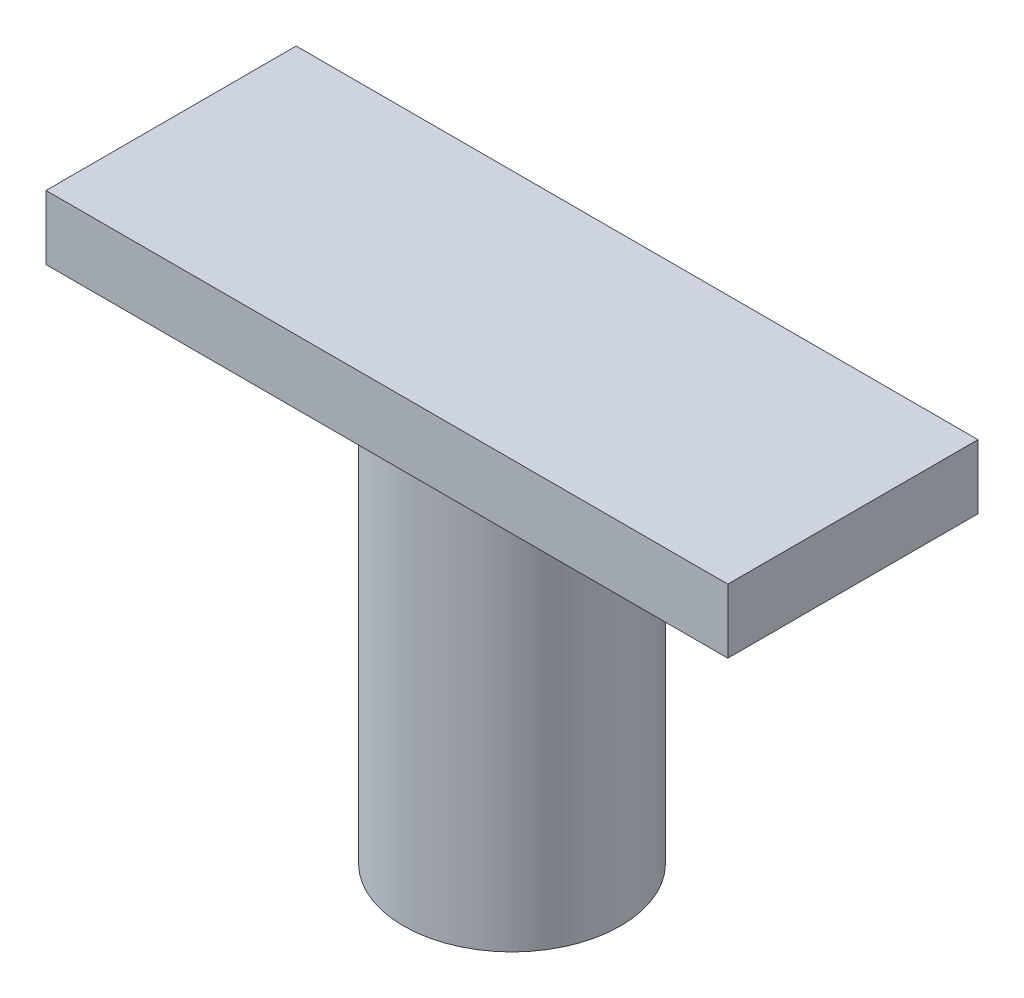
SolidWorks part; units mm, degrees
ref_plane "Front Plane" through (0, 0, 0) normal (0, 0, 1) x (1, 0, 0)
ref_plane "Top Plane" through (0, 0, 0) normal (0, 1, 0) x (1, 0, 0)
ref_plane "Right Plane" through (0, 0, 0) normal (1, 0, 0) x (0, 0, -1)
sketch "Sketch1" plane through (0, 0, 0) normal (0, 1, 0) x (1, 0, 0)
  circle A0 centre (22.7298, -8.2396) radius 16.9166
extrude "Boss-Extrude1" add sketch "Sketch1" along normal blind 64
sketch "Sketch2" plane through (0, 64, 0) normal (0, 1, 0) x (1, 0, 0)
  line L1 (-30.4017, -27.7334) -> (75.8613, -27.7334)
  line L2 (-30.4017, -27.7334) -> (-30.4017, 11.2543)
  line L3 (-30.4017, 11.2543) -> (75.8613, 11.2543)
  line L4 (75.8613, -27.7334) -> (75.8613, 11.2543)
  line L5 (-30.4017, -27.7334) -> (75.8613, 11.2543) construction
  line L6 (-30.4017, 11.2543) -> (75.8613, -27.7334) construction
  circle A0 centre (22.7298, -8.2396) radius 16.9166 construction
  point P0 (22.7298, -8.2396)
extrude "Boss-Extrude2" add sketch "Sketch2" along normal blind 10
